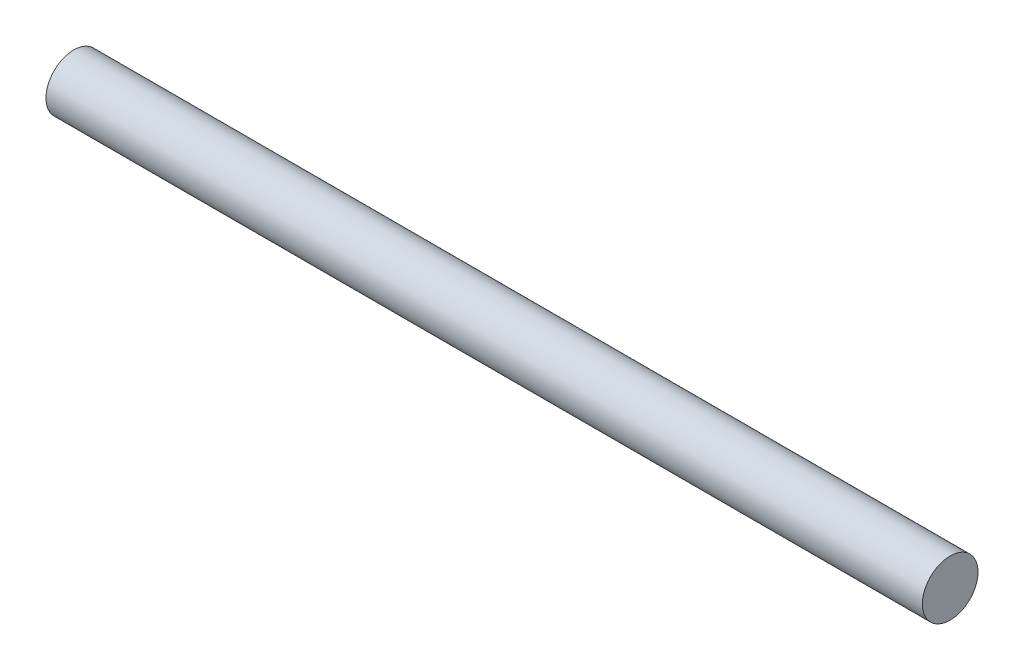
SolidWorks part; units mm, degrees
ref_plane "Alzado" through (0, 0, 0) normal (0, 0, 1) x (1, 0, 0)
ref_plane "Planta" through (0, 0, 0) normal (0, 1, 0) x (1, 0, 0)
ref_plane "Vista lateral" through (0, 0, 0) normal (1, 0, 0) x (0, 0, -1)
sketch "Croquis1" plane through (0, 0, 0) normal (1, 0, 0) x (0, 0, -1)
  circle A0 centre (0, 0) radius 12.7
  dimension "D1" = 25.4
extrude "Saliente-Extruir1" add sketch "Croquis1" along normal blind 400
sketch "Croquis2" plane through (0, 0, 0) normal (-1, 0, 0) x (0, 0, 1)
  circle A0 centre (0, 0) radius 4.7625
  dimension "D1" = 9.525
extrude "Cortar-Extruir1" cut sketch "Croquis2" against normal blind 30
sketch "Croquis3" plane through (400, 0, 0) normal (1, 0, 0) x (0, 0, -1)
  circle A0 centre (0, 0) radius 11.9062
  circle A1 centre (0, 0) radius 12.7
  circle A2 centre (0, 0) radius 12.7 construction
  dimension "D1" = 0.7937
